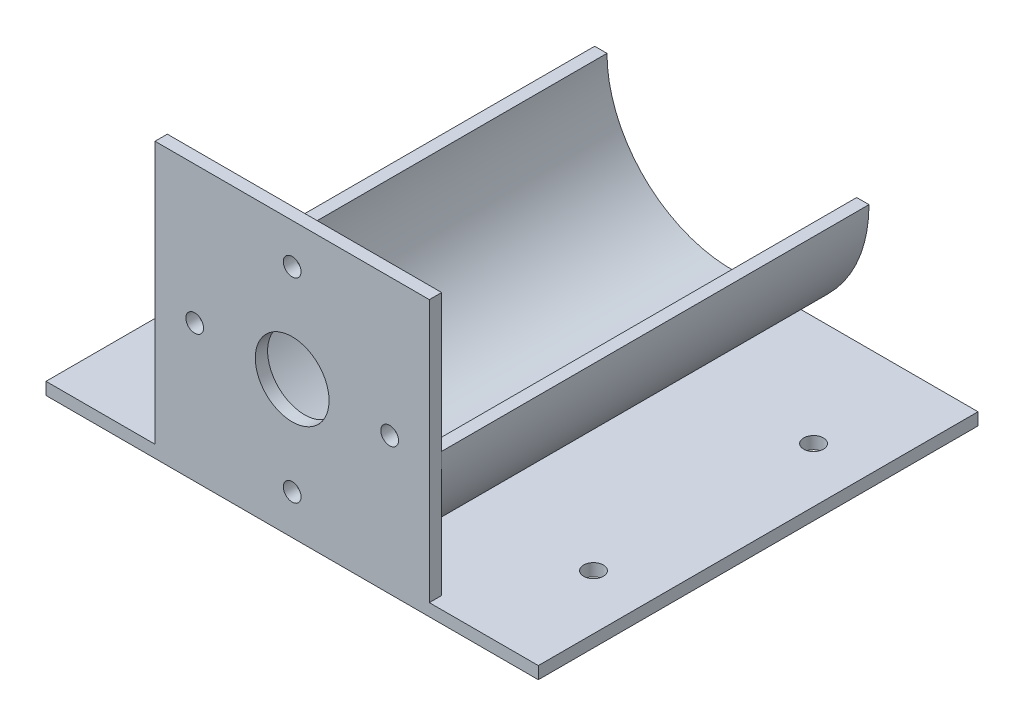
SolidWorks part; units mm, degrees
ref_plane "Front" through (0, 0, 0) normal (0, 0, 1) x (1, 0, 0)
ref_plane "Top" through (0, 0, 0) normal (0, 1, 0) x (1, 0, 0)
ref_plane "Right" through (0, 0, 0) normal (1, 0, 0) x (0, 0, -1)
sketch "Sketch1" plane through (0, 0, 0) normal (0, 0, 1) x (1, 0, 0)
  line L0 (-35.3822, 0) -> (-32.2072, 0)
  line L5 (32.2072, 0) -> (35.3822, 0)
  line L7 (-63.5, -35.3822) -> (63.5, -35.3822)
  line L8 (-63.5, -35.3822) -> (-63.5, -32.2072)
  line L9 (-63.5, -32.2072) -> (63.5, -32.2072)
  line L10 (63.5, -35.3822) -> (63.5, -32.2072)
  arc A0 (-32.2072, 0) -> (32.2072, 0) centre (0, 0) ccw
  arc A1 (-35.3822, 0) -> (35.3822, 0) centre (0, 0) ccw
  point P10 (0, 0)
  point P11 (0, -32.2072)
  dimension "D1" = 64.4144
  dimension "D2" = 70.7644
  dimension "D3" = 127
  dimension "D4" = 3.175
extrude "Boss-Extrude2" add sketch "Sketch1" along normal blind 110.236 contours A1 L7 L10 L9 | A1 L9 L8 L7
sketch "Sketch2" plane through (0, 0, 110.236) normal (0, 0, 1) x (1, 0, 0)
  line L0 (-63.5, -35.3822) -> (63.5, -35.3822) construction
  line L1 (-35.3822, -35.3822) -> (35.3822, -35.3822)
  line L2 (-35.3822, -32.2072) -> (-35.3822, 35.4838)
  line L3 (-35.3822, 35.4838) -> (35.3822, 35.4838)
  line L4 (35.3822, -32.2072) -> (35.3822, 35.4838)
  line L5 (-35.3822, -35.3822) -> (-63.5, -35.3822)
  line L6 (-63.5, -35.3822) -> (-63.5, -32.2072)
  line L7 (-63.5, -32.2072) -> (-35.3822, -32.2072)
  line L8 (-63.5, -32.2072) -> (-14.6491, -32.2072) construction
  line L9 (35.3822, -35.3822) -> (63.5, -35.3822)
  line L10 (63.5, -35.3822) -> (63.5, -32.2072)
  line L11 (63.5, -32.2072) -> (35.3822, -32.2072)
  line L12 (14.6491, -32.2072) -> (63.5, -32.2072) construction
  circle A1 centre (-25.146, 0) radius 2.286
  circle A2 centre (0, 25.146) radius 2.286
  circle A3 centre (25.146, 0) radius 2.286
  circle A4 centre (0, -25.146) radius 2.286
  circle A5 centre (0, 0) radius 9.5123
  point P34 (0, 0)
  dimension "D2" = 7.0612
  dimension "D4" = 4.572
  dimension "D5" = 19.0246
  dimension "D1" = 67.691
  dimension "D3" = 4
extrude "Boss-Extrude3" add sketch "Sketch2" along normal blind 3.175
sketch "Sketch3" plane through (0, -32.2072, 0) normal (0, 1, 0) x (1, 0, 0)
  line L0 (63.5, -113.411) -> (63.5, 0) construction
  line L1 (35.3822, -113.411) -> (-35.3822, -113.411) construction
  line L2 (0, 0) -> (0, -113.411) construction
  line L3 (63.5, -56.7055) -> (-63.5, -56.7055) construction
  line L4 (-63.5, -113.411) -> (-63.5, 0) construction
  circle A0 centre (49.403, -85.09) radius 2.54
  circle A1 centre (49.403, -28.321) radius 2.54
  circle A2 centre (-49.403, -85.09) radius 2.54
  circle A3 centre (-49.403, -28.321) radius 2.54
  point P4 (63.5, -56.7055)
  dimension "D1" = 5.08
  dimension "D2" = 28.3845
  dimension "D3" = 14.097
extrude "Cut-Extrude1" cut sketch "Sketch3" against normal through all
